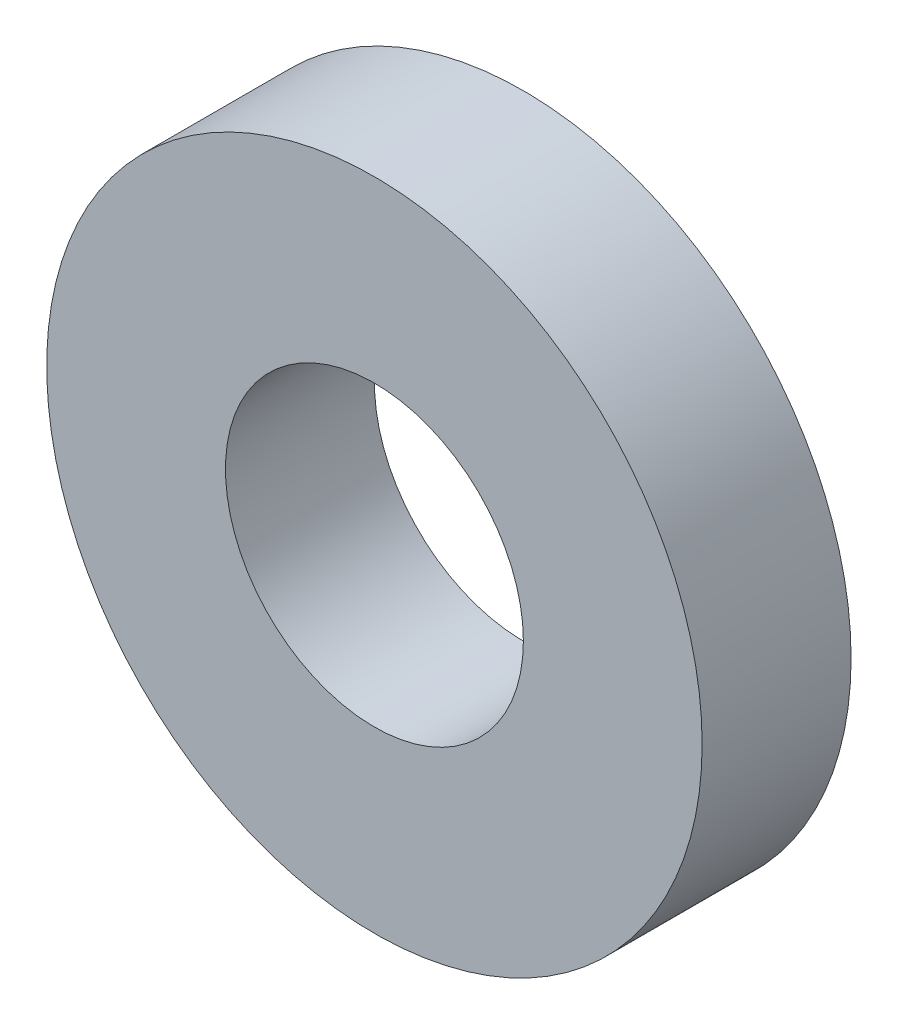
SolidWorks part; units mm, degrees
ref_plane "Front Plane" through (0, 0, 0) normal (0, 0, 1) x (1, 0, 0)
ref_plane "Top Plane" through (0, 0, 0) normal (0, 1, 0) x (1, 0, 0)
ref_plane "Right Plane" through (0, 0, 0) normal (1, 0, 0) x (0, 0, -1)
sketch "Sketch1" plane through (0, 0, 0) normal (0, 0, 1) x (1, 0, 0)
  circle A0 centre (0, 0) radius 6
  circle A1 centre (0, 0) radius 13.2
extrude "Boss-Extrude1" add sketch "Sketch1" along normal blind 6
sketch "Sketch2" plane through (0, 0, 6) normal (0, 0, 1) x (1, 0, 0)
  line L0 (0, 0) -> (0, 15.2) construction
  line L1 (-1.8199, 15.2) -> (0, 0) construction
  line L2 (1.8199, 15.2) -> (0, 0) construction
  arc A0 (-6.8199, 12) -> (6.8199, 12) centre (0, 0) cw
  arc A1 (-1.8199, 13.2) -> (1.8199, 13.2) centre (0, 0) cw
  arc A2 (-1.8199, 10.512) -> (1.8199, 10.512) centre (0, 0) cw
